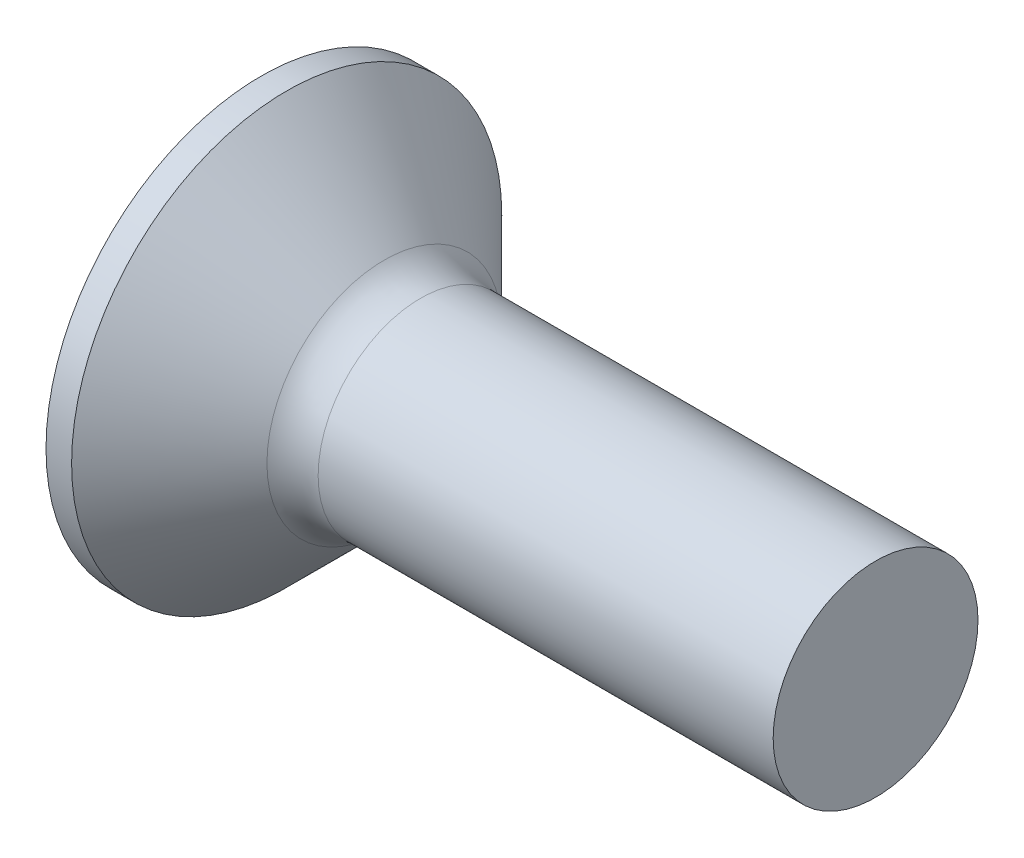
SolidWorks part; units mm, degrees
ref_plane "Plane1" through (0, 0, 0) normal (0, 0, 1) x (1, 0, 0)
ref_plane "Plane2" through (0, 0, 0) normal (0, 1, 0) x (1, 0, 0)
ref_plane "Plane3" through (0, 0, 0) normal (1, 0, 0) x (0, 0, -1)
sketch "BodySke" plane through (0, 0, 0) normal (0, 0, 1) x (1, 0, 0)
  line L0 (0, 0) -> (0, 4.2)
  line L1 (0, 4.2) -> (0.5, 4.2)
  line L2 (2.7, 2) -> (12, 2)
  line L3 (12, 2) -> (12, 0)
  line L4 (12, 0) -> (0, 0)
  line L5 (-6.35, 0) -> (82.55, 0) construction
  line L6 (2.7, -2) -> (12, -2) construction
  line L7 (0.5, -4.2) -> (2.7, -2) construction
  line L8 (0.5, 4.2) -> (2.7, 2)
  line L9 (0, -4.2) -> (0.5, -4.2) construction
  line L10 (3.4, 3.5875) -> (3.4, -5.9375) construction
  line L11 (0, 6.35) -> (0, -3.175) construction
  dimension "Diameter" = 4
  dimension "Length" = 12
  dimension "Head_ht" = 2.7
  dimension "Head_dia" = 8.4
  dimension "Head_ang" = 90
  dimension "D6" = 0.5
  dimension "Advance" = 0.7
  dimension "Thread_nom" = 12
revolve "Base-Revolve" add sketch "BodySke"
cosmetic thread "ThreadCosmetic" [suppressed]
fillet "Fillet1" radius 1 1 edges at (2.7, 0, 2)
sketch "Sketch3" plane through (0, 0, 0) normal (-1, 0, 0) x (0, 0, 1)
  line L0 (-0.515, 2.2) -> (0.515, 2.2)
  line L1 (0.515, 2.2) -> (0.515, -2.2)
  line L2 (0.515, -2.2) -> (-0.515, -2.2)
  line L3 (-0.515, -2.2) -> (-0.515, 2.2)
  dimension "D1" = 2.2
  dimension "Cross_dia" = 4.4
  dimension "D2" = 0.515
  dimension "Cross_width" = 1.03
ref_plane "Plane4" through (2.51, 0, 0) normal (-1, 0, 0) x (0, 0, 1)
sketch "Sketch4" plane through (2.51, 0, 0) normal (-1, 0, 0) x (0, 0, 1)
  line L0 (-0.515, 0.9486) -> (0.515, 0.9486)
  line L3 (0.515, 0.9486) -> (0.515, -0.9486)
  line L4 (0.515, -0.9486) -> (-0.515, -0.9486)
  line L5 (-0.515, -0.9486) -> (-0.515, 0.9486)
  dimension "D1" = 1.03
  dimension "D2" = 1.8971
  dimension "D3" = 0.515
  dimension "D4" = 0.9486
loft "Recess" cut profiles "Sketch3", "Sketch4"
pattern_circular "RecPat" count 2 every 90 about axis through (0, 0, 0) along (1, 0, 0) of "Recess"
sketch "RecCorSke" plane through (0, 0, 0) normal (0, 0, 1) x (1, 0, 0)
  line L0 (-3.175, 0) -> (15.875, 0) construction
  line L2 (0, 0) -> (0, 1.0265)
  line L3 (0, 1.0265) -> (2.51, 0.851)
  line L4 (2.51, 0.851) -> (2.7865, 0)
  line L5 (2.7865, 0) -> (0, 0)
  dimension "Diameter" = 1.702
  dimension "Depth" = 2.51
  dimension "Draft_angle" = 4
  dimension "Bottom_angle" = 18
revolve "RecessCore" cut sketch "RecCorSke" angle 360 about L0
sketch "ThdSchSke" plane through (0, 0, 0) normal (0, 0, 1) x (1, 0, 0)
  line L0 (3.4, -1.61) -> (3.1269, -2)
  line L1 (3.4, -1.61) -> (3.6731, -2)
  line L2 (3.6731, -2) -> (3.6731, -2.5)
  line L3 (-3.175, 0) -> (5.1513, 0) construction
  line L5 (3.6731, -2.5) -> (3.1269, -2.5)
  line L6 (3.1269, -2.5) -> (3.1269, -2)
  line L7 (0, 4.2) -> (0, -4.2) construction
  dimension "Thread_minor" = 3.22
  dimension "Diameter" = 4
  dimension "Start" = 3.4
  dimension "SideAngle" = 55
  dimension "VeeAngle" = 70
  dimension "Overcut" = 5
revolve "ThreadSchematic" [suppressed] cut sketch "ThdSchSke" angle 360 about L3
pattern_linear "ThdSchPat" [suppressed]
equation "\"D1@Sketch3\" = \"Cross_dia@Sketch3\" / 2"
equation "\"D2@Sketch3\" = \"Cross_width@Sketch3\" / 2"
equation "\"Depth@RecCorSke\" = \"Cross_depth@Plane4\""
equation "\"D1@Sketch4\" = \"Cross_width@Sketch3\""
equation "\"D2@Sketch4\" = \"Cross_dia@Sketch3\" - 2.0 * \"Cross_depth@Plane4\" * tan(26.5  * 0.017453292)"
equation "\"D3@Sketch4\" = \"D1@Sketch4\" / 2"
equation "\"D4@Sketch4\" = \"D2@Sketch4\" / 2"
equation "\"Thread_length@ThreadCosmetic\" = ((sgn( (\"Length@BodySke\" - \"Advance@BodySke\" * 1.0 - \"Head_ht@BodySke\" ) - \"Thread_nom@BodySke\" )-1)*( (\"Length@BodySke\" - \"Advance@BodySke\" * 1.0 - \"Head_ht@BodySke\" ) - \"Thread_nom@BodySke\" ))/-2+ \"Thread_nom@BodySke\""
equation "\"Thread_minor@ThdSchSke\" = \"Thread_minor@ThreadCosmetic\""
equation "\"Diameter@ThdSchSke\" = \"Diameter@BodySke\""
equation "\"Overcut@ThdSchSke\" = \"Diameter@BodySke\" * 1.25"
equation "\"Start@ThdSchSke\" = 0.000001 + \"Length@BodySke\" - \"Thread_length@ThreadCosmetic\"  '---Countersunk---"
equation "\"Num_threads@ThdSchPat\" = int( \"Thread_length@ThreadCosmetic\" / \"Advance@BodySke\" + 0.999 )  + 1"
equation "\"Advance@ThdSchPat\" = \"Thread_length@ThreadCosmetic\" /  (\"Num_threads@ThdSchPat\" - 1) 'relax it"
